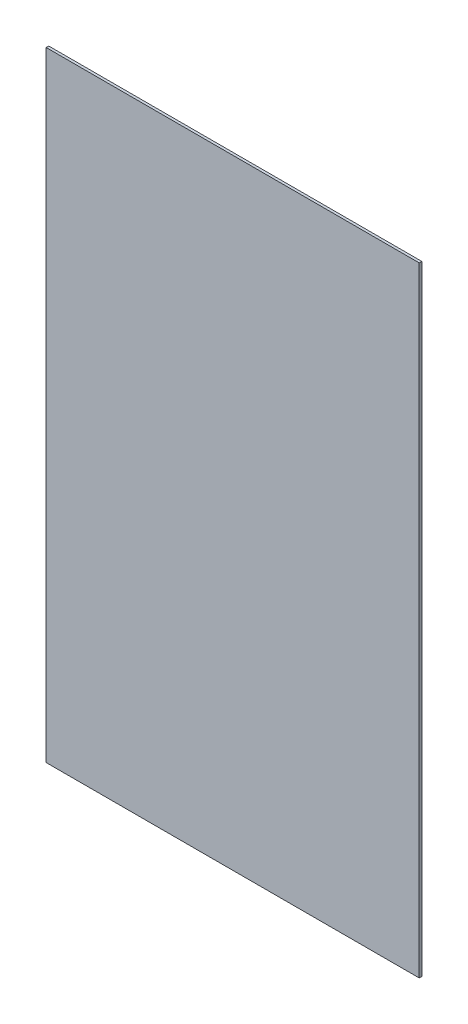
SolidWorks part; units mm, degrees
ref_plane "Front Plane" through (0, 0, 0) normal (0, 0, 1) x (1, 0, 0)
ref_plane "Top Plane" through (0, 0, 0) normal (0, 1, 0) x (1, 0, 0)
ref_plane "Right Plane" through (0, 0, 0) normal (1, 0, 0) x (0, 0, -1)
sketch "Sketch1" plane through (0, 0, 0) normal (0, 0, 1) x (1, 0, 0)
  line L1 (0, 0) -> (457.2, 0)
  line L2 (0, 0) -> (0, 758.9266)
  line L3 (0, 758.9266) -> (457.2, 758.9266)
  line L4 (457.2, 0) -> (457.2, 758.9266)
  dimension "D1" = 457.2
  dimension "D2" = 758.9266
extrude "Boss-Extrude1" add sketch "Sketch1" along normal blind 3.175
